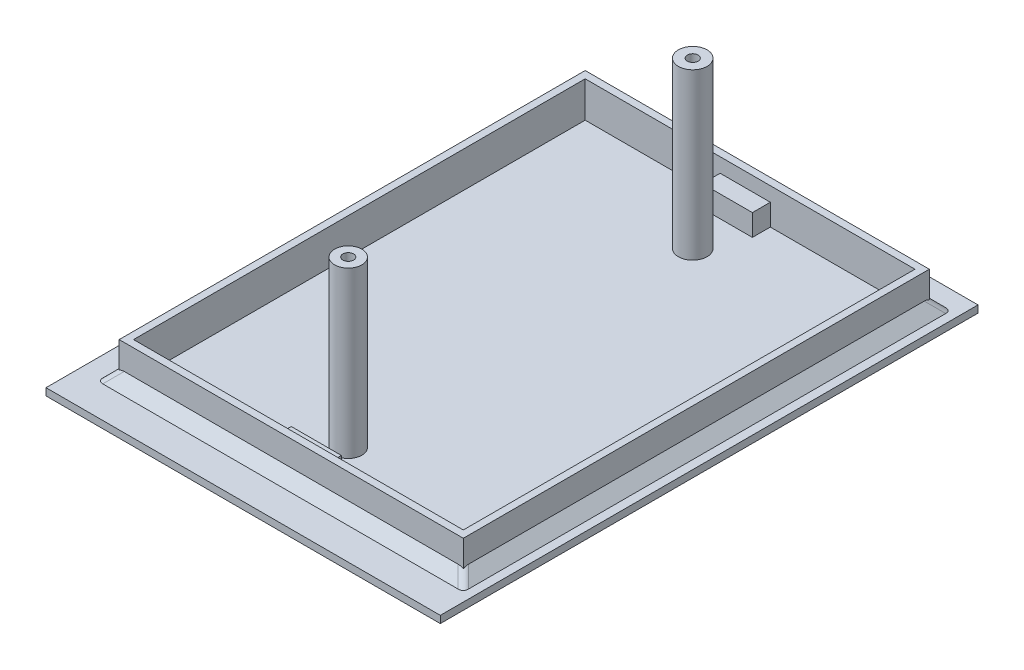
SolidWorks part; units mm, degrees
ref_plane "Спереди" through (0, 0, 0) normal (0, 0, 1) x (1, 0, 0)
ref_plane "Сверху" through (0, 0, 0) normal (0, 1, 0) x (1, 0, 0)
ref_plane "Справа" through (0, 0, 0) normal (1, 0, 0) x (0, 0, -1)
sketch "Эскиз1" plane through (0, 0, 0) normal (0, 1, 0) x (1, 0, 0)
  line L1 (-26.8693, 21.4902) -> (28.1307, 21.4902)
  line L2 (-26.8693, 21.4902) -> (-26.8693, -53.5098)
  line L3 (-26.8693, -53.5098) -> (28.1307, -53.5098)
  line L4 (28.1307, 21.4902) -> (28.1307, -53.5098)
  dimension "D1" = 55
  dimension "D2" = 75
extrude "Бобышка-Вытянуть1" add sketch "Эскиз1" against normal blind 1
sketch "Эскиз3" plane through (0, 0, 0) normal (0, 1, 0) x (1, 0, 0)
  line L1 (-22.5761, 17.4061) -> (25.4239, 17.4061)
  line L2 (-22.5761, 17.4061) -> (-22.5761, -47.5939)
  line L3 (-22.5761, -47.5939) -> (25.4239, -47.5939)
  line L4 (25.4239, 17.4061) -> (25.4239, -47.5939)
  line L5 (-21.5761, 16.4061) -> (24.4239, 16.4061)
  line L6 (-21.5761, 16.4061) -> (-21.5761, -46.5939)
  line L7 (-21.5761, -46.5939) -> (24.4239, -46.5939)
  line L8 (24.4239, 16.4061) -> (24.4239, -46.5939)
  dimension "D1" = 48
  dimension "D2" = 65
  dimension "D3" = 1
  dimension "D4" = 1
  dimension "D5" = 1
  dimension "D6" = 1
extrude "Бобышка-Вытянуть2" add sketch "Эскиз3" along normal blind 5
sketch "Эскиз4" plane through (0, 0, 0) normal (0, 1, 0) x (1, 0, 0)
  line L0 (-21.5761, -46.5939) -> (24.4239, -46.5939) construction
  line L1 (4.9239, -46.5939) -> (-2.0761, -46.5939)
  line L2 (4.9239, -46.5939) -> (4.9239, -44.0939)
  line L3 (4.9239, -44.0939) -> (-2.0761, -44.0939)
  line L4 (-2.0761, -46.5939) -> (-2.0761, -44.0939)
  line L5 (24.4239, 16.4061) -> (-21.5761, 16.4061) construction
  line L6 (-2.7541, 16.4061) -> (4.2459, 16.4061)
  line L7 (-2.7541, 16.4061) -> (-2.7541, 13.9061)
  line L8 (-2.7541, 13.9061) -> (4.2459, 13.9061)
  line L9 (4.2459, 16.4061) -> (4.2459, 13.9061)
  line L10 (-21.5761, 16.4061) -> (-21.5761, -46.5939) construction
  line L11 (24.4239, -46.5939) -> (24.4239, 16.4061) construction
  dimension "D1" = 7
  dimension "D2" = 2.5
  dimension "D3" = 7
  dimension "D4" = 2.5
  dimension "D5" = 18.822
  dimension "D6" = 19.5
extrude "Бобышка-Вытянуть3" add sketch "Эскиз4" along normal blind 3
sketch "Эскиз5" plane through (0, 0, 0) normal (0, 1, 0) x (1, 0, 0)
  line L0 (-21.5761, -46.5939) -> (24.4239, -46.5939) construction
  line L1 (-21.5761, 16.4061) -> (-21.5761, -46.5939) construction
  circle A0 centre (1.4239, -39.6439) radius 1.9
  dimension "D1" = 6.95
  dimension "D2" = 23
extrude "Бобышка-Вытянуть4" add sketch "Эскиз5" along normal blind 23
sketch "Эскиз6" plane through (0, 23, 0) normal (0, 1, 0) x (1, 0, 0)
  circle A0 centre (1.4239, -39.6439) radius 0.75
  circle A1 centre (1.4239, -39.6439) radius 1.9 construction
  dimension "D1" = 0
  dimension "D2" = 0
extrude "Вырез-Вытянуть1" cut sketch "Эскиз6" against normal blind 10
sketch "Эскиз7" plane through (0, 0, 0) normal (0, 1, 0) x (1, 0, 0)
  line L0 (24.4239, 16.4061) -> (4.2459, 16.4061) construction
  line L1 (24.4239, -46.5939) -> (24.4239, 16.4061) construction
  circle A0 centre (1.4239, 8.4061) radius 2
  dimension "D1" = 8
  dimension "D2" = 23
extrude "Бобышка-Вытянуть5" add sketch "Эскиз7" along normal blind 23
sketch "Эскиз8" plane through (0, 23, 0) normal (0, 1, 0) x (1, 0, 0)
  circle A0 centre (1.4239, 8.4061) radius 0.75
  circle A1 centre (1.4239, 8.4061) radius 2 construction
  dimension "D1" = 0
  dimension "D2" = 0
extrude "Вырез-Вытянуть2" cut sketch "Эскиз8" against normal blind 10
chamfer "Фаска1" distance 1.5 angle 45 4 edges at (1.4239, 0, 47.5939) (25.4239, 0, 15.0939) (1.4239, 0, -17.4061) (-22.5761, 0, 15.0939)
fillet "Скругление2" radius 1 4 edges at (26.1739, 0.75, 48.3439) (-23.3261, 0.75, 48.3439) (-23.3261, 0.75, -18.1561) (26.1739, 0.75, -18.1561)
equation "\"D4@Эскиз3\"=\"D3@Эскиз3\""
equation "\"D5@Эскиз3\"=\"D3@Эскиз3\""
equation "\"D6@Эскиз3\"=\"D3@Эскиз3\""
